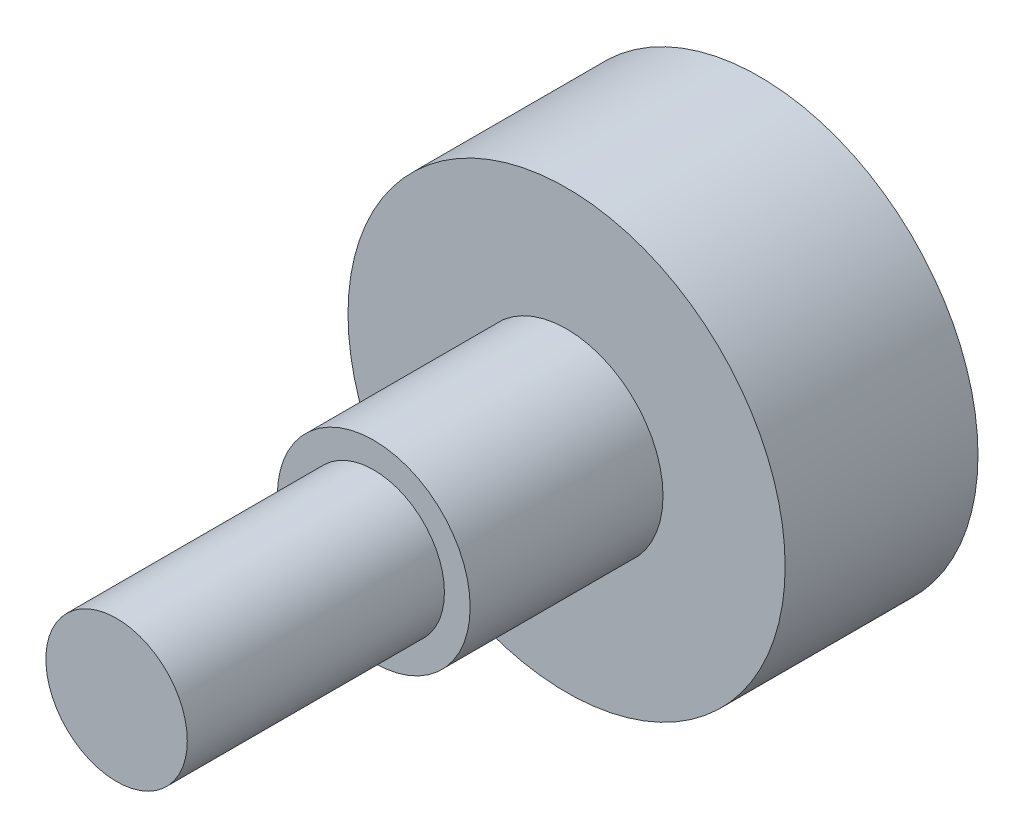
SolidWorks part; units mm, degrees
ref_plane "Plan de face" through (0, 0, 0) normal (0, 0, 1) x (1, 0, 0)
ref_plane "Plan de dessus" through (0, 0, 0) normal (0, 1, 0) x (1, 0, 0)
ref_plane "Plan de droite" through (0, 0, 0) normal (1, 0, 0) x (0, 0, -1)
sketch "Esquisse1" plane through (0, 0, 0) normal (0, 0, 1) x (1, 0, 0)
  circle A0 centre (0, 0) radius 8.5
  dimension "D1" = 17
extrude "Boss.-Extru.1" add sketch "Esquisse1" along normal blind 7.5
sketch "Esquisse2" plane through (0, 0, 7.5) normal (0, 0, 1) x (1, 0, 0)
  circle A0 centre (0, 0) radius 3.75
  dimension "D1" = 7.5
extrude "Boss.-Extru.2" add sketch "Esquisse2" along normal blind 7.5
sketch "Esquisse3" plane through (0, 0, 15) normal (0, 0, 1) x (1, 0, 0)
  circle A0 centre (0, 0) radius 2.75
  dimension "D1" = 5.5
extrude "Boss.-Extru.3" add sketch "Esquisse3" along normal blind 10
